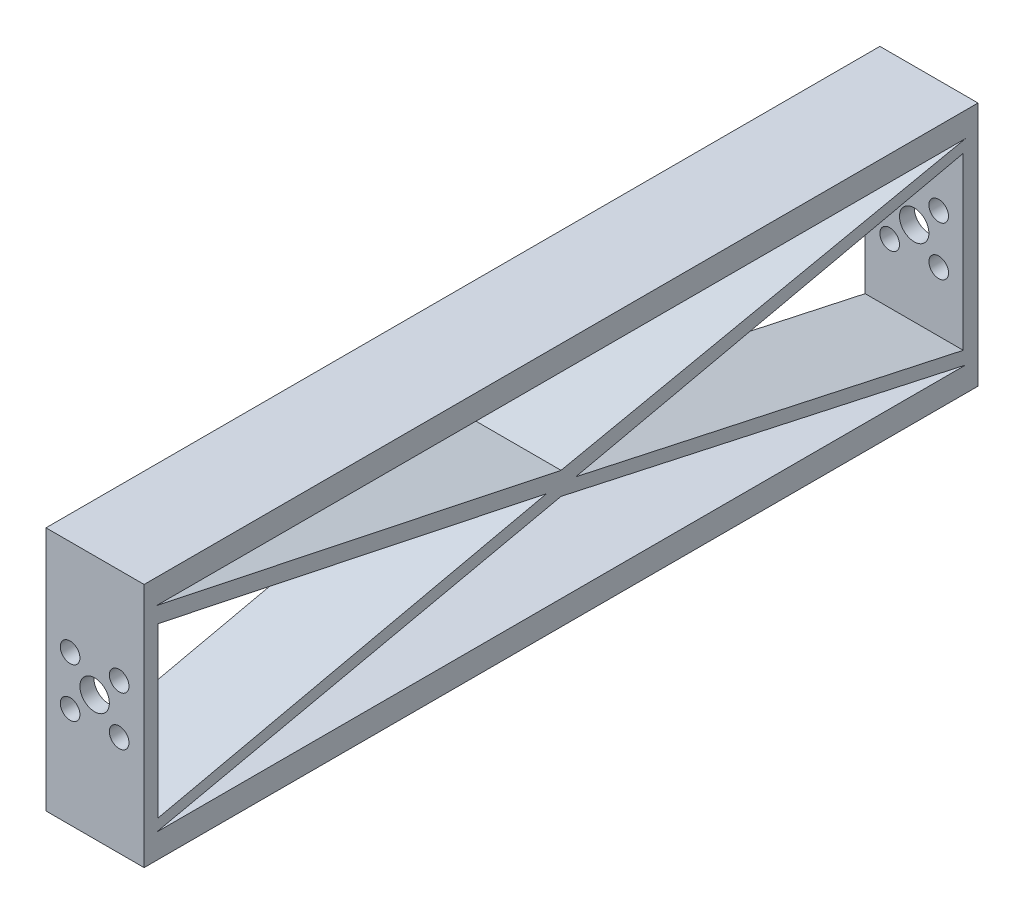
SolidWorks part; units mm, degrees
ref_plane "Front Plane" through (0, 0, 0) normal (0, 0, 1) x (1, 0, 0)
ref_plane "Top Plane" through (0, 0, 0) normal (0, 1, 0) x (1, 0, 0)
ref_plane "Right Plane" through (0, 0, 0) normal (1, 0, 0) x (0, 0, -1)
sketch "Sketch4" plane through (0, 0, 0) normal (1, 0, 0) x (0, 0, -1)
  line L1 (-85, 25) -> (85, 25)
  line L2 (-85, 25) -> (-85, -25)
  line L3 (-85, -25) -> (85, -25)
  line L4 (85, 25) -> (85, -25)
  line L5 (-85, 25) -> (85, -25) construction
  line L6 (-85, -25) -> (85, 25) construction
  point P0 (0, 0)
extrude "Boss-Extrude1" add sketch "Sketch4" along normal blind 20
sketch "Sketch5" plane through (0, 0, 0) normal (-1, 0, 0) x (0, 0, 1)
  line L0 (-82.5, -20) -> (0, -1.9577)
  line L1 (-82.5, 20) -> (82.5, 20)
  line L2 (-82.5, 20) -> (-82.5, -20)
  line L3 (-82.5, -20) -> (82.5, -20)
  line L4 (82.5, 20) -> (82.5, -20)
  line L5 (0, -1.9577) -> (82.5, -20)
  line L6 (0, 2.6486) -> (82.5, 20)
  line L7 (-82.5, 20) -> (0, 2.6486)
  point P0 (0, 0)
extrude "Cut-Extrude5" cut sketch "Sketch5" against normal blind 20 contours L1 L7 L6 | L5 L0 L3
sketch "Sketch6" plane through (0, 0, 0) normal (-1, 0, 0) x (0, 0, 1)
  line L0 (-2.9941, 0) -> (-81.9927, 17.6192)
  line L1 (-2.9941, 0) -> (-81.9927, -17.1586)
  line L2 (-81.9927, 17.6192) -> (-81.9927, -17.1586)
  line L3 (2.9941, 0) -> (82.1486, 16.6477)
  line L4 (2.9941, 0) -> (82.1486, -17.654)
  line L5 (82.1486, 16.6477) -> (82.1486, -17.654)
extrude "Cut-Extrude6" cut sketch "Sketch6" against normal blind 20
sketch "Sketch7" plane through (0, 0, 85) normal (0, 0, 1) x (1, 0, 0)
  circle A0 centre (9.9155, 0.479) radius 3
  circle A1 centre (4.9155, -4.521) radius 2
  circle A2 centre (14.9155, -4.521) radius 2
  circle A3 centre (14.9155, 5.479) radius 2
  circle A4 centre (4.9155, 5.479) radius 2
extrude "Cut-Extrude7" cut sketch "Sketch7" against normal blind 5
sketch "Sketch8" plane through (0, 0, -85) normal (0, 0, -1) x (-1, 0, 0)
  circle A0 centre (-10, 0) radius 3
  circle A1 centre (-15, 5) radius 2
  circle A2 centre (-5, 5) radius 2
  circle A3 centre (-5, -5) radius 2
  circle A4 centre (-15, -5) radius 2
extrude "Cut-Extrude8" cut sketch "Sketch8" against normal blind 5
